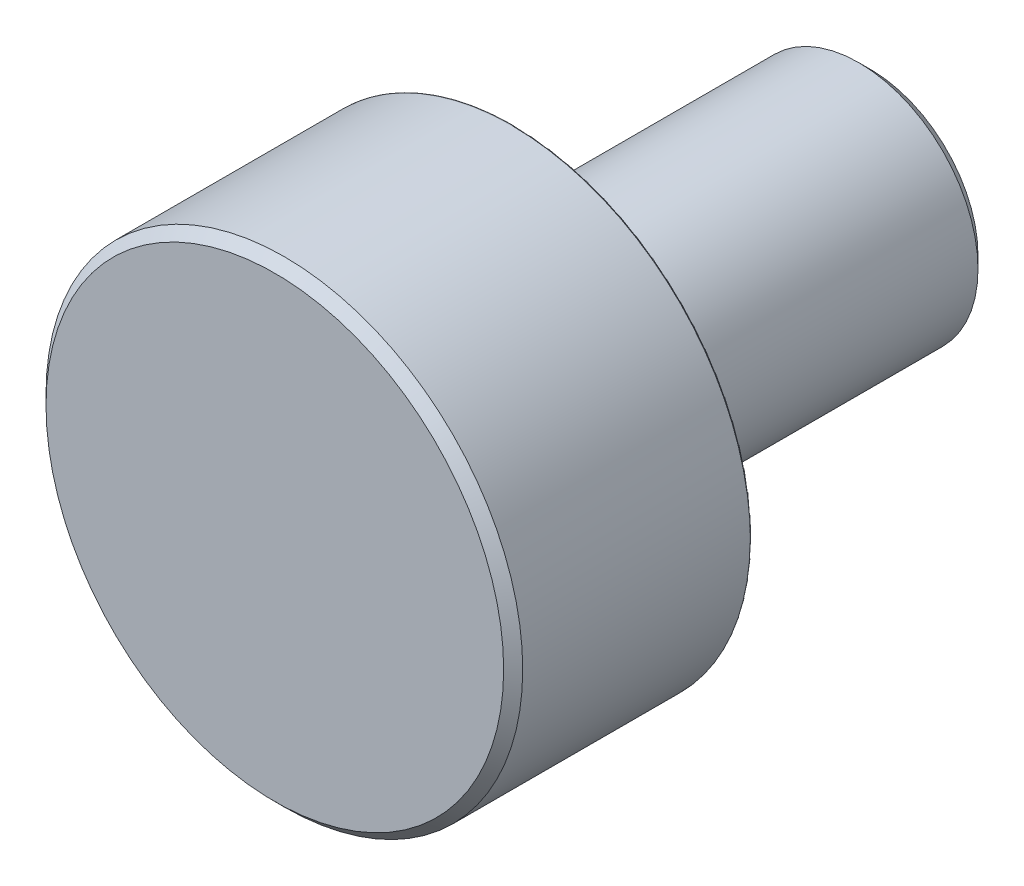
SolidWorks part; units mm, degrees
ref_plane "Front" through (0, 0, 0) normal (0, 0, 1) x (1, 0, 0)
ref_plane "Top" through (0, 0, 0) normal (0, 1, 0) x (1, 0, 0)
ref_plane "Right" through (0, 0, 0) normal (1, 0, 0) x (0, 0, -1)
sketch "Sketch0" plane through (0, 0, 0) normal (1, 0, 0) x (0, 0, -1)
  line L0 (-8, 0) -> (0, 0)
  line L1 (0, 0) -> (12, 0)
  line L2 (-12.7, 0) -> (49987.3, 0) construction
  line L3 (12, 0) -> (12, 4)
  line L4 (-8, 0) -> (-8, 8)
  line L5 (12, -4) -> (12, 4)
  line L6 (0, 0) -> (0, 8)
  point P10 (12, 0)
  point P13 (0, 8)
  dimension "Stud Length" = 12
  dimension "Stud Dia" = 8
  dimension "Dia" = 16
  dimension "Length" = 8
sketch "Sketch1" plane through (0, 0, 0) normal (1, 0, 0) x (0, 0, -1)
  line L0 (12, 0) -> (12, 4) construction
  line L1 (-8, 0) -> (-8, 8)
  line L2 (-8, 8) -> (-0.05, 8)
  line L3 (0, 7.95) -> (0, 4.4472)
  line L4 (0, 3.6) -> (0.8, 3.6)
  line L5 (0.8, 3.6) -> (0.8, 4)
  line L6 (0.8, 4) -> (12, 4)
  line L7 (12, 4) -> (12, 0)
  line L8 (12, 0) -> (-8, 0)
  arc A0 (0, 3.6) -> (-0.0444, 4.3975) centre (0, 4) cw
  arc A1 (-0.0444, 4.3975) -> (0, 4.4472) centre (-0.05, 4.4472) ccw
  arc A2 (-0.05, 8) -> (0, 7.95) centre (-0.05, 7.95) cw
  point P22 (0, 4.4)
  dimension "D4" = 0.05
  dimension "D5" = 0.05
  dimension "D2" = 0.8
  dimension "D1" = 0.4
  dimension "D3" = 0.8
revolve "Revolve1" add sketch "Sketch1" angle 360 about L2
chamfer "Chamfer1" distance 0.32 angle 45 1 edges at (8, 0, 8)
chamfer "Chamfer2" distance 0.4 angle 45 1 edges at (4, 0, -12)
equation "\"D1@Sketch1\"=\"D2@Sketch1\"/2"
equation "\"D2@Sketch1\" = \"Dia@Sketch0\" * .05"
equation "\"D1@Chamfer1\"=\"Dia@Sketch0\" * .02"
equation "\"D1@Chamfer2\" = \"Stud Dia@Sketch0\" * .05"
equation "\"D3@Sketch1\"=\"D1@Sketch1\"*2"
